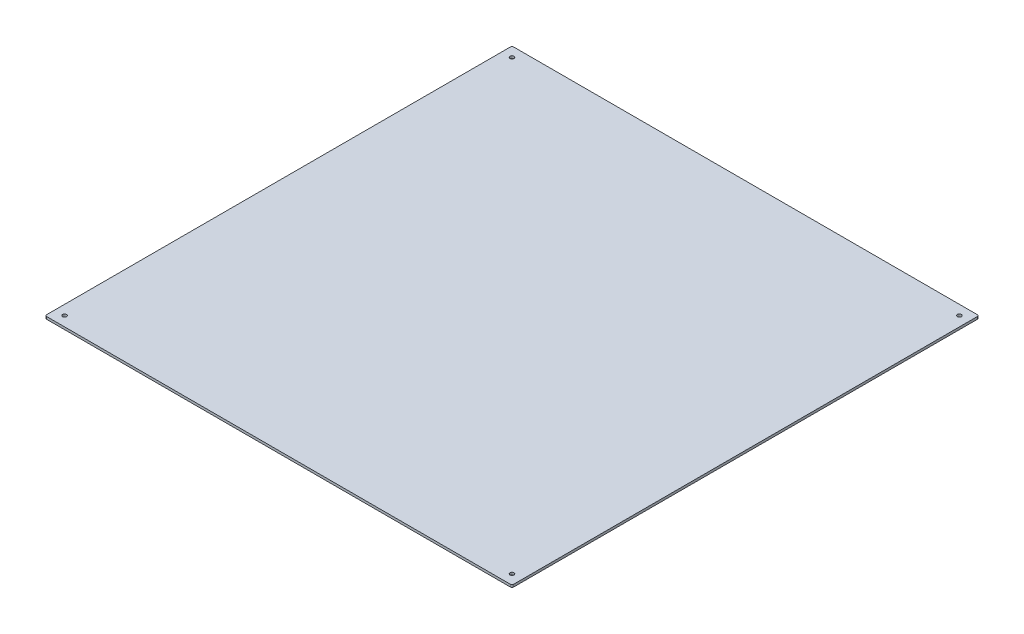
SolidWorks part; units mm, degrees
material "PC High Viscosity"
ref_plane "Front Plane" through (0, 0, 0) normal (0, 0, 1) x (1, 0, 0)
ref_plane "Top Plane" through (0, 0, 0) normal (0, 1, 0) x (1, 0, 0)
ref_plane "Right Plane" through (0, 0, 0) normal (1, 0, 0) x (0, 0, -1)
sketch "Sketch1" plane through (0, 0, 0) normal (0, 1, 0) x (1, 0, 0)
  line L1 (304.7, -304.7) -> (-304.7, -304.7)
  line L2 (304.7, -304.7) -> (304.7, 304.7)
  line L3 (304.7, 304.7) -> (-304.7, 304.7)
  line L4 (-304.7, -304.7) -> (-304.7, 304.7)
  line L5 (304.7, -304.7) -> (-304.7, 304.7) construction
  line L6 (304.7, 304.7) -> (-304.7, -304.7) construction
  line L7 (304.8, -304.8) -> (-304.8, -304.8)
  line L8 (304.8, -304.8) -> (304.8, 304.8)
  line L9 (304.8, 304.8) -> (-304.8, 304.8)
  line L10 (-304.8, -304.8) -> (-304.8, 304.8)
  line L11 (304.8, -304.8) -> (-304.8, 304.8) construction
  line L12 (304.8, 304.8) -> (-304.8, -304.8) construction
  point P0 (0, 0)
  point P6 (0, 0)
  point P7 (0, 0)
  dimension "D1" = 609.4
  dimension "D2" = 609.4
  dimension "D3" = 609.6
  dimension "D4" = 609.6
extrude "Boss-Extrude2" add sketch "Sketch1" along normal blind 3.175 contours L10 L7 L8 L9 L1 L4 L3 L2 | L4 L1 L2 L3
hole_wizard "#5 (0.2055) Diameter Hole1" positions "Sketch2" profile "Sketch3" hole size "#5" standard "ANSI Inch" end condition through all
sketch "Sketch2" plane through (0, 0, 0) normal (0, -1, 0) x (-1, 0, 0)
  line L2 (-304.7, 304.7) -> (304.7, 304.7) construction
  line L3 (-304.7, -304.7) -> (-304.7, 304.7) construction
  line L4 (0, 1.7463) -> (0, -1.7463) construction
  line L5 (-1.7463, 0) -> (1.7463, 0) construction
  point P0 (-292, 292)
  point P541 (292, 292)
  point P545 (292, -292)
  point P546 (-292, -292)
  point P547 (-292, 292)
  dimension "D1" = 12.7
  dimension "D2" = 12.7
sketch "Sketch3" plane through (292, 0, -292) normal (1, 0, 0) x (0, 0, -1)
  line L0 (0, 0) -> (0, 3.175)
  line L1 (0, 3.175) -> (2.6098, 3.175)
  line L2 (2.6098, 3.175) -> (2.6098, 0)
  line L5 (2.6098, 0) -> (0, 0)
  line L11 (0, -6.35) -> (0, 107.95) construction
  dimension "Thru Hole Dia." = 5.2197
  dimension "Thru Hole Depth" = 3.175
fillet "Fillet1" radius 2.1082 4 edges at (-304.8, 1.5875, -304.8) (-304.8, 1.5875, 304.8) (304.8, 1.5875, 304.8) (304.8, 1.5875, -304.8)
hole_wizard "1/2 (0.5) Diameter Hole1" positions "Sketch4" profile "Sketch5" hole size "1/2" standard "ANSI Inch"
sketch "Sketch4" plane through (0, 0, 0) normal (0, -1, 0) x (-1, 0, 0)
  line L3 (-302.6918, -304.8) -> (302.6918, -304.8) construction
  point P0 (0, -254)
  dimension "D1" = 50.8
sketch "Sketch5" plane through (0, 0, 254) normal (1, 0, 0) x (0, 0, -1)
  line L0 (0, 0) -> (0, 3.175)
  line L1 (0, 3.175) -> (6.35, 3.175)
  line L2 (6.35, 3.175) -> (6.35, 0)
  line L5 (6.35, 0) -> (0, 0)
  line L11 (0, -6.35) -> (0, 107.95) construction
  dimension "Thru Hole Dia." = 12.7
  dimension "Thru Hole Depth" = 3.175
hole_wizard "1 (1) Diameter Hole2" positions "Sketch6" profile "Sketch7" hole size "1" standard "ANSI Inch"
sketch "Sketch6" plane through (0, 0, 0) normal (0, -1, 0) x (-1, 0, 0)
  circle A0 centre (0, -254) radius 6.35 construction
  circle A1 centre (0, -254) radius 6.35
  point P0 (63.5, -254)
  dimension "D1" = 63.5
sketch "Sketch7" plane through (-63.5, 0, 254) normal (1, 0, 0) x (0, 0, -1)
  line L0 (0, 0) -> (0, 3.175)
  line L1 (0, 3.175) -> (12.7, 3.175)
  line L2 (12.7, 3.175) -> (12.7, 0)
  line L5 (12.7, 0) -> (0, 0)
  line L11 (0, -6.35) -> (0, 107.95) construction
  dimension "Thru Hole Dia." = 25.4
  dimension "Thru Hole Depth" = 3.175
equation "\"D2@Sketch2\"=\"D1@Sketch2\""
